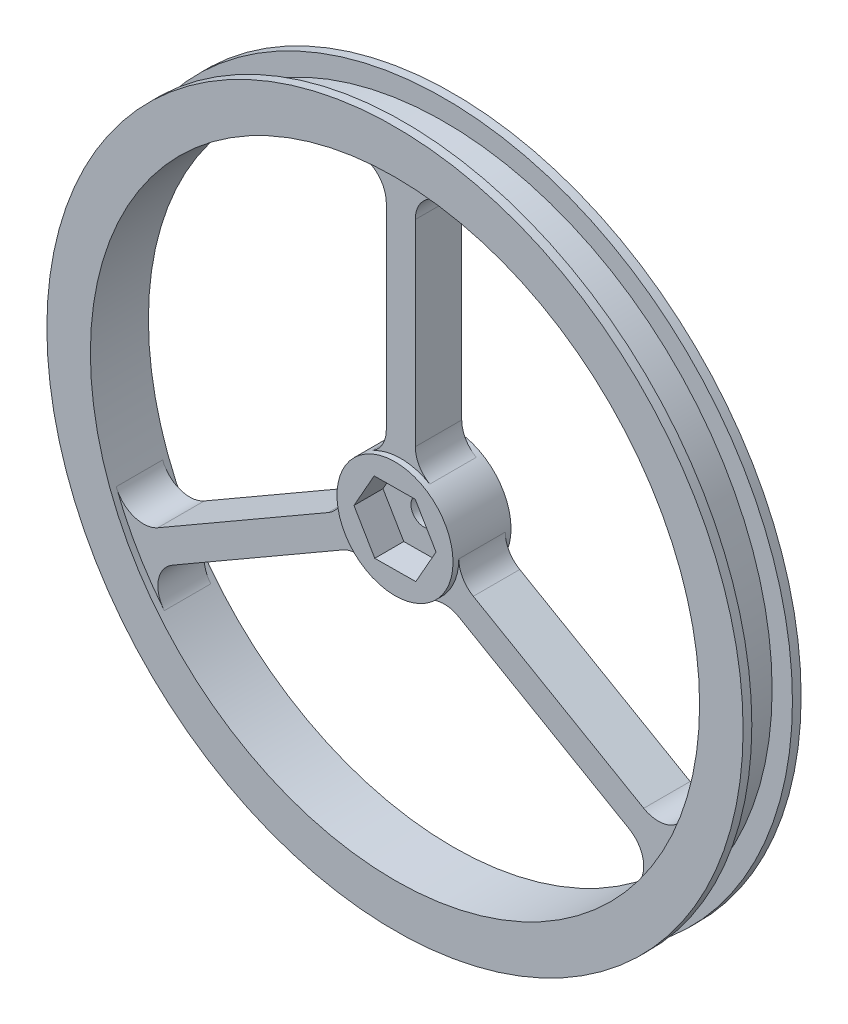
SolidWorks part; units mm, degrees
ref_plane "Front Plane" through (0, 0, 0) normal (0, 0, 1) x (1, 0, 0)
ref_plane "Top Plane" through (0, 0, 0) normal (0, 1, 0) x (1, 0, 0)
ref_plane "Right Plane" through (0, 0, 0) normal (1, 0, 0) x (0, 0, -1)
sketch "Sketch1" plane through (0, 0, 0) normal (0, 0, 1) x (1, 0, 0)
  line L0 (0, 0) -> (0, 36.6729) construction
  line L1 (0, 0) -> (-38.6006, -22.2861) construction
  line L2 (0, 0) -> (53.8821, -31.1088) construction
  line L3 (-1.27, 23.8273) -> (-1.27, 6.5991)
  line L4 (1.27, 23.8273) -> (1.27, 6.5991)
  line L5 (21.2701, -10.8138) -> (6.35, -2.1997)
  line L6 (20.0001, -13.0135) -> (5.08, -4.3994)
  line L7 (-20.0001, -13.0135) -> (-5.08, -4.3994)
  line L8 (-21.2701, -10.8138) -> (-6.35, -2.1997)
  circle A0 centre (0, 0) radius 30.48
  circle A1 centre (0, 0) radius 1.143
  arc A2 (-4.2111, 26.3355) -> (-24.9127, -9.5208) centre (0, 0) ccw
  arc A3 (-2.54, 4.3994) -> (-5.08, 0) centre (0, 0) ccw
  arc A4 (5.08, 0) -> (2.54, 4.3994) centre (0, 0) ccw
  arc A5 (-2.54, -4.3994) -> (2.54, -4.3994) centre (0, 0) ccw
  arc A6 (-20.7016, -16.8146) -> (20.7016, -16.8146) centre (0, 0) ccw
  arc A7 (24.9127, -9.5208) -> (4.2111, 26.3355) centre (0, 0) ccw
  arc A8 (-1.27, 23.8273) -> (-4.2111, 26.3355) centre (-3.81, 23.8273) ccw
  arc A9 (4.2111, 26.3355) -> (1.27, 23.8273) centre (3.81, 23.8273) ccw
  arc A10 (-24.9127, -9.5208) -> (-21.2701, -10.8138) centre (-22.5401, -8.6141) ccw
  arc A11 (-20.0001, -13.0135) -> (-20.7016, -16.8146) centre (-18.7301, -15.2132) ccw
  arc A12 (20.0001, -13.0135) -> (20.7016, -16.8146) centre (18.7301, -15.2132) cw
  arc A13 (21.2701, -10.8138) -> (24.9127, -9.5208) centre (22.5401, -8.6141) ccw
  arc A14 (-1.27, 6.5991) -> (-2.54, 4.3994) centre (-3.81, 6.5991) cw
  arc A15 (1.27, 6.5991) -> (2.54, 4.3994) centre (3.81, 6.5991) ccw
  arc A16 (6.35, -2.1997) -> (5.08, 0) centre (7.62, 0) cw
  arc A17 (-5.08, -4.3994) -> (-2.54, -4.3994) centre (-3.81, -6.5991) cw
  arc A18 (5.08, -4.3994) -> (2.54, -4.3994) centre (3.81, -6.5991) ccw
  arc A19 (-6.35, -2.1997) -> (-5.08, 0) centre (-7.62, 0) ccw
  point P23 (0, 0)
  dimension "D1" = 2.286
  dimension "D2" = 60.96
  dimension "D3" = 53.34
  dimension "D4" = 10.16
  dimension "D10" = 2.54
  dimension "D11" = 2.54
  dimension "D12" = 2.54
  dimension "D13" = 2.54
  dimension "D14" = 2.54
  dimension "D15" = 2.54
  dimension "D16" = 2.54
  dimension "D17" = 2.54
  dimension "D18" = 2.54
  dimension "D19" = 2.54
  dimension "D20" = 2.54
  dimension "D21" = 2.54
  dimension "D5" = 120
  dimension "D6" = 120
  dimension "D8" = 2.54
  dimension "D9" = 1.27
  dimension "D7" = 3
extrude "Boss-Extrude1" add sketch "Sketch1" along normal blind 5.08
sketch "Sketch2" plane through (0, 0, 5.08) normal (0, 0, 1) x (1, 0, 0)
  line L1 (1.7706, 3.1263) -> (-1.8221, 3.0965)
  line L2 (-1.8221, 3.0965) -> (-3.5927, -0.0297)
  line L3 (-3.5927, -0.0297) -> (-1.7706, -3.1263)
  line L4 (-1.7706, -3.1263) -> (1.8221, -3.0965)
  line L5 (1.8221, -3.0965) -> (3.5927, 0.0297)
  line L6 (3.5927, 0.0297) -> (1.7706, 3.1263)
  circle A0 centre (0, 0) radius 3.1115 construction
  point P1 (-0.0257, 3.1114)
  dimension "D1" = 6.223
extrude "Cut-Extrude1" cut sketch "Sketch2" against normal blind 2.54
sketch "Sketch3" plane through (0, 0, 0) normal (1, 0, 0) x (0, 0, -1)
  line L0 (0, 30.48) -> (-5.08, 30.48) construction
  line L1 (-4.318, 30.48) -> (-0.762, 30.48)
  line L2 (-4.318, 30.48) -> (-4.318, 28.702)
  line L3 (-4.318, 28.702) -> (-0.762, 28.702)
  line L4 (-0.762, 30.48) -> (-0.762, 28.702)
  line L5 (-5.08, 30.48) -> (-5.08, -30.48) construction
  line L6 (0, -30.48) -> (0, 30.48) construction
  line L7 (-7.9179, 0) -> (4.7802, 0) construction
  dimension "D1" = 0.762
  dimension "D2" = 0.762
  dimension "D3" = 1.778
revolve "Cut-Revolve1" cut sketch "Sketch3" angle 360 about L7
sketch "Sketch6" plane through (0, 0, 0) normal (0, 0, 1) x (1, 0, 0)
  circle A0 centre (0, 0) radius 26.67
  circle A1 centre (0, 0) radius 5.08
  dimension "D1" = 53.34
  dimension "D2" = 10.16
extrude "Cut-Extrude2" cut sketch "Sketch6" along normal blind 0.508
sketch "Sketch8" plane through (0, 0, 5.08) normal (0, 0, 1) x (1, 0, 0)
  circle A0 centre (0, 0) radius 26.67
  circle A1 centre (0, 0) radius 5.08
  dimension "D1" = 53.34
  dimension "D2" = 10.16
extrude "Cut-Extrude3" cut sketch "Sketch8" against normal blind 0.508
